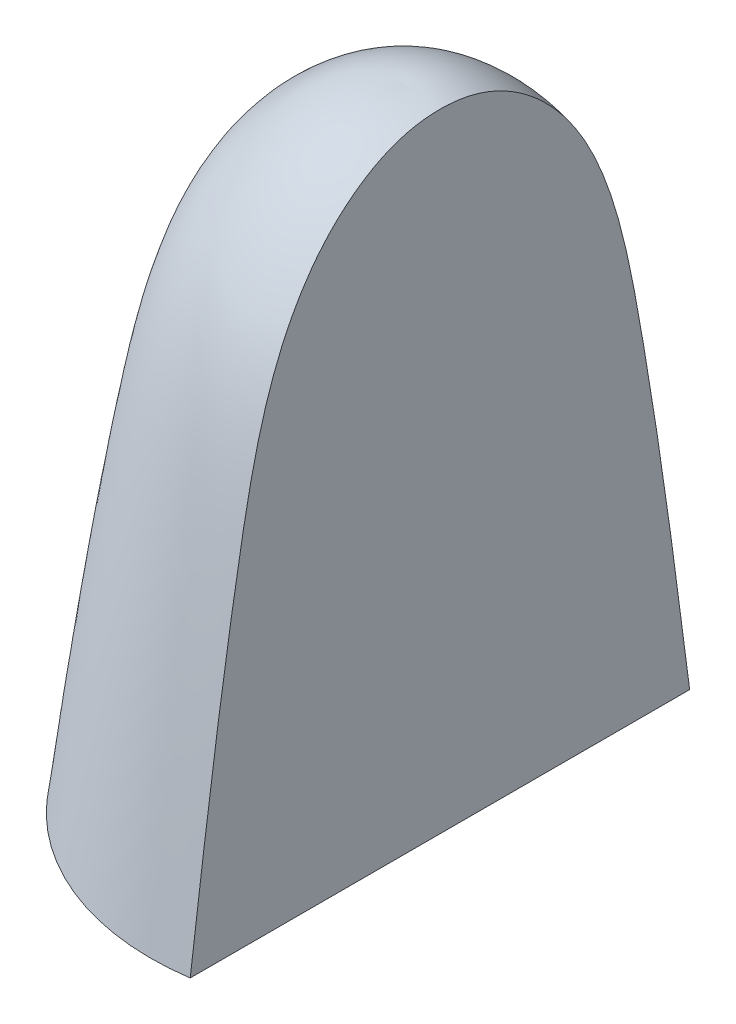
SolidWorks part; units mm, degrees
ref_plane "Plan de face" through (0, 0, 0) normal (0, 0, 1) x (1, 0, 0)
ref_plane "Plan de dessus" through (0, 0, 0) normal (0, 1, 0) x (1, 0, 0)
ref_plane "Plan de droite" through (0, 0, 0) normal (1, 0, 0) x (0, 0, -1)
sketch "Sketch1" plane through (0, 0, 0) normal (0, 0, 1) x (1, 0, 0)
  line L0 (0, 18.0579) -> (0, 5.5898) construction
  line L1 (4.88, 0) -> (6.88, 0)
  line L2 (0, 17.2) -> (0, 15.4)
  arc A0 (4.88, 0) -> (4.88, 1.6062) centre (-7.5884, 0.8031) ccw
  spline S0 degree 3 poles (6.88, 0) (6.4769, 3.1777) (5.8089, 8.3578) (4.3783, 15.4646) (1.1111, 17.2802) (0, 17.2) knots 0 0 0 0 0.473755 0.838492 1 1 1 1
  spline S1 degree 2 poles (0, 15.4) (1.563, 15.2978) (2.2842, 13.6332) knots 0 0 0 1 1 1
  spline S2 degree 2 poles (2.2842, 13.6332) (4.2663, 7.7784) (4.88, 1.6062) knots 0 0 0 1 1 1
  dimension "D4" = 2
  dimension "D1" = 15.4
  dimension "D2" = 2
  dimension "D3" = 1.8
  dimension "D5" = 4.88
revolve "Revolve1" add sketch "Sketch1" angle 360 about L0
sketch "Sketch2" plane through (0, 0, 0) normal (0, 1, 0) x (1, 0, 0)
  circle A1 centre (0, 0) radius 0.5
sketch3d "3DSketch1"
  point P0 (-2.2452, 9.2133, -5.0907)
ref_plane "Plane2" through (7, 0, 0) normal (1, 0, 0) x (0, 0, -1)
sketch "Sketch5" plane through (0, 0, 0) normal (0, -1, 0) x (1, 0, 0)
  line L1 (2, 9.912) -> (7, 9.912)
  line L2 (2, 9.912) -> (2, -8.088)
  line L3 (2, -8.088) -> (7, -8.088)
  line L4 (7, 9.912) -> (7, -8.088)
  line L5 (2, 9.912) -> (7, -8.088) construction
  line L6 (2, -8.088) -> (7, 9.912) construction
  circle A0 centre (0, 0) radius 6.88 construction
  point P0 (4.5, 0.912)
  dimension "D1" = 2
  dimension "D2" = 18
  dimension "D3" = 5
extrude "Cut-Extrude4" cut sketch "Sketch5" against normal blind 20
sketch "Sketch9" plane through (0, 0, 0) normal (0, 0, 1) x (1, 0, 0)
  line L0 (0, 17.2) -> (0, 0)
  line L1 (4.88, 0) -> (6.88, 0)
  line L3 (0, 0) -> (4.88, 0)
  spline S0 degree 3 poles (6.88, 0) (6.4769, 3.1777) (5.8089, 8.3578) (4.3783, 15.4646) (1.1111, 17.2802) (0, 17.2) knots 0 0 0 0 0.473755 0.838492 1 1 1 1
  dimension "D2" = 2
revolve "Revolve3" add sketch "Sketch9" angle 90 about L0 other way angle 90
ref_plane "Plane4" through (10, 0, 0) normal (1, 0, 0) x (0, 0, -1)
sketch "Sketch12" plane through (10, 0, 0) normal (1, 0, 0) x (0, 0, -1)
  line L1 (-7.579, 18.113) -> (7.579, 18.113)
  line L2 (-7.579, 18.113) -> (-7.579, -0.8499)
  line L3 (-7.579, -0.8499) -> (7.579, -0.8499)
  line L4 (7.579, 18.113) -> (7.579, -0.8499)
  line L5 (-7.579, 18.113) -> (7.579, -0.8499) construction
  line L6 (-7.579, -0.8499) -> (7.579, 18.113) construction
  point P0 (0, 8.6315)
extrude "Cut-Extrude5" cut sketch "Sketch12" against normal blind 9
ref_plane "Plane5" through (0, 20, 0) normal (0, 1, 0) x (1, 0, 0)
sketch "Sketch15" plane through (0, 0, 0) normal (0, 0, 1) x (1, 0, 0)
  line L0 (0, 18.0579) -> (0, 5.5898) construction
  line L1 (4.88, 0) -> (6.88, 0)
  line L2 (0, 17.2) -> (0, 15.4)
  arc A0 (4.88, 0) -> (4.88, 1.6062) centre (-7.5884, 0.8031) ccw
  spline S0 degree 3 poles (6.88, 0) (6.4769, 3.1777) (5.8089, 8.3578) (4.3783, 15.4646) (1.1111, 17.2802) (0, 17.2) knots 0 0 0 0 0.473755 0.838492 1 1 1 1
  spline S1 degree 2 poles (0, 15.4) (1.563, 15.2978) (2.2842, 13.6332) knots 0 0 0 1 1 1
  spline S2 degree 2 poles (2.2842, 13.6332) (4.2663, 7.7784) (4.88, 1.6062) knots 0 0 0 1 1 1
  dimension "D4" = 2
  dimension "D2" = 2
  dimension "D3" = 1.8
